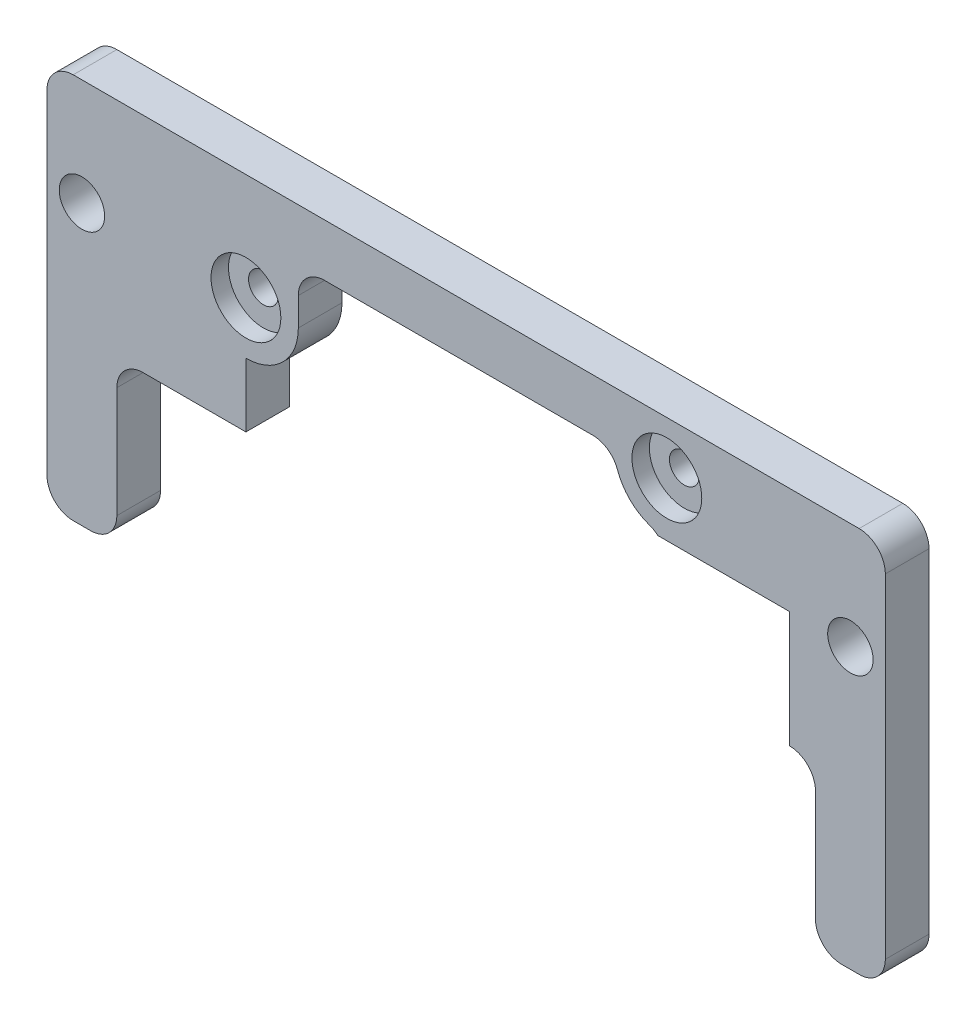
SolidWorks part; units mm, degrees
ref_plane "Plan de face" through (0, 0, 0) normal (0, 0, 1) x (1, 0, 0)
ref_plane "Plan de dessus" through (0, 0, 0) normal (0, 1, 0) x (1, 0, 0)
ref_plane "Plan de droite" through (0, 0, 0) normal (1, 0, 0) x (0, 0, -1)
sketch "Esquisse1" plane through (0, 0, 0) normal (0, 0, 1) x (1, 0, 0)
  line L1 (7, -13.3122) -> (81, -13.3122)
  line L2 (-12.0449, 12.22) -> (107.2676, 12.22) construction
  line L4 (-1, 12.22) -> (89, 12.22)
  line L7 (92, 9.22) -> (92, -29)
  line L8 (-1, -32) -> (1, -32)
  line L9 (4, -29) -> (4, -16.3122)
  line L11 (89, -32) -> (87, -32)
  line L12 (84, -29) -> (84, -16.3122)
  line L13 (-4, 24.1839) -> (-4, -45.9272) construction
  line L14 (92, 13.3122) -> (92, -47.924) construction
  line L15 (-4, 9.22) -> (-4, -29)
  circle A0 centre (0, 0) radius 2.6
  circle A1 centre (88, 0) radius 2.6
  circle A2 centre (18.7795, 0) radius 1.7
  circle A3 centre (66.9795, 6.22) radius 1.7
  arc A4 (-1, 12.22) -> (-4, 9.22) centre (-1, 9.22) ccw
  arc A5 (89, 12.22) -> (92, 9.22) centre (89, 9.22) cw
  arc A6 (92, -29) -> (89, -32) centre (89, -29) cw
  arc A7 (87, -32) -> (84, -29) centre (87, -29) cw
  arc A8 (84, -16.3122) -> (81, -13.3122) centre (81, -16.3122) ccw
  arc A9 (4, -16.3122) -> (7, -13.3122) centre (7, -16.3122) cw
  arc A10 (1, -32) -> (4, -29) centre (1, -29) ccw
  arc A11 (-4, -29) -> (-1, -32) centre (-1, -29) ccw
  point P9 (43.4072, 0)
  point P32 (-4, 12.22)
  point P35 (92, 12.22)
  point P38 (92, -32)
  point P41 (84, -32)
  point P48 (4, -32)
  point P51 (-4, -32)
  dimension "D1" = 88
  dimension "D2" = 6.22
  dimension "D8" = 3
  dimension "D3" = 48.2
  dimension "D4" = 74
  dimension "D5" = 4
  dimension "D7" = 8
  dimension "D9" = 6
extrude "Boss.-Extru.1" add sketch "Esquisse1" along normal blind 5
sketch "Esquisse2" plane through (0, 0, 5) normal (0, 0, 1) x (1, 0, 0)
  circle A0 centre (18.7795, 0) radius 4
  circle A1 centre (66.9795, 6.22) radius 4
extrude "Enlèv. mat.-Extru.1" cut sketch "Esquisse2" against normal blind 2
sketch "Esquisse3" plane through (0, 0, 5) normal (0, 0, 1) x (1, 0, 0)
  line L0 (18.7795, 0) -> (18.7795, -13.3122) construction
  line L1 (7, -13.3122) -> (81, -13.3122) construction
  line L2 (66.9795, -2.2653) -> (66.9795, -13.3122) construction
  line L3 (66.9795, 6.22) -> (18.7795, 6.22) construction
  line L4 (18.7795, 0) -> (27.5601, -8.8936) construction
  line L5 (18.7795, 0) -> (30.2929, 0) construction
  line L6 (18.7795, -6) -> (18.7795, -10.3122)
  line L7 (21.7795, -13.3122) -> (63.9795, -13.3122)
  line L8 (18.7795, -10.3122) -> (18.7795, -13.3122)
  line L9 (58.4943, 6.22) -> (27.7795, 6.22)
  line L10 (24.7795, 3.22) -> (24.7795, 0)
  line L11 (30.2929, 0) -> (88, 0) construction
  line L12 (88, 0) -> (88, -13.3122) construction
  line L13 (88, -13.3122) -> (63.9795, -13.3122) construction
  line L14 (81, -13.3122) -> (63.9795, -13.3122)
  line L15 (81, -13.3122) -> (81, 0)
  line L16 (81, 0) -> (65.9464, 0)
  line L17 (18.7795, -13.3122) -> (21.7795, -13.3122)
  arc A0 (18.7795, -6) -> (24.7795, 0) centre (18.7795, 0) ccw
  arc A1 (64.9795, 0.5631) -> (61.3227, 4.22) centre (66.9795, 6.22) cw
  arc A4 (64.9795, 0.5631) -> (65.9464, 0) centre (63.9795, -2.2653) cw
  arc A5 (61.3227, 4.22) -> (58.4943, 6.22) centre (58.4943, 3.22) ccw
  arc A6 (27.7795, 6.22) -> (24.7795, 3.22) centre (27.7795, 3.22) ccw
  point P25 (66.9795, 0.22)
  point P28 (60.9795, 6.22)
  point P31 (24.7795, 6.22)
  point P41 (88, -5.1967)
  point P44 (84.8033, 0)
extrude "Enlèv. mat.-Extru.2" cut sketch "Esquisse3" against normal blind 5
